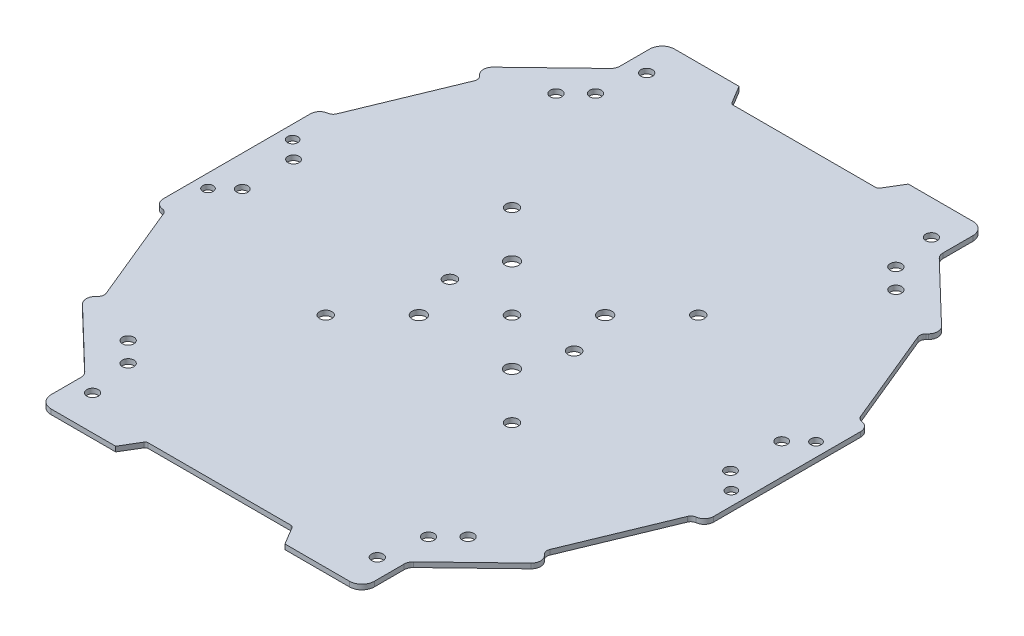
SolidWorks part; units mm, degrees
ref_plane "Front Plane" through (0, 0, 0) normal (0, 0, 1) x (1, 0, 0)
ref_plane "Top Plane" through (0, 0, 0) normal (0, 1, 0) x (1, 0, 0)
ref_plane "Right Plane" through (0, 0, 0) normal (1, 0, 0) x (0, 0, -1)
ref_plane "Plane1"
sketch "Sketch1" plane through (0, 0, 0) normal (0, 1, 0) x (-1, 0, 0)
  line L0 (74.0875, 321.0883) -> (70.3692, 327.2855)
  line L1 (70.3692, 327.2855) -> (45.5805, 327.2855)
  line L2 (45.5805, 327.2855) -> (45.5805, 312.4122)
  line L3 (45.5805, 312.4122) -> (23.246, 290.9343)
  line L4 (23.246, 290.9343) -> (26.6825, 287.3608)
  line L5 (26.6825, 287.3608) -> (12.7354, 253.539)
  line L6 (12.7354, 253.539) -> (9.0171, 253.539)
  line L7 (9.0171, 253.539) -> (9.0171, 226.8911)
  line L8 (9.0171, 226.8911) -> (9.0171, 200.2432)
  line L9 (9.0171, 200.2432) -> (12.7354, 200.2432)
  line L10 (12.7354, 200.2432) -> (26.6825, 166.4214)
  line L11 (26.6825, 166.4214) -> (23.246, 162.8479)
  line L12 (23.246, 162.8479) -> (45.5805, 141.37)
  line L13 (45.5805, 141.37) -> (45.5805, 126.4967)
  line L14 (45.5805, 126.4967) -> (70.3692, 126.4967)
  line L15 (70.3692, 126.4967) -> (74.0875, 132.6939)
  line L16 (74.0875, 132.6939) -> (97.6368, 132.6939)
  line L17 (97.6368, 132.6939) -> (121.1861, 132.6939)
  line L18 (121.1861, 132.6939) -> (124.9044, 126.4967)
  line L19 (124.9044, 126.4967) -> (149.6932, 126.4967)
  line L20 (149.6932, 126.4967) -> (149.6932, 141.37)
  line L21 (149.6932, 141.37) -> (172.0276, 162.8479)
  line L22 (172.0276, 162.8479) -> (168.5911, 166.4214)
  line L23 (168.5911, 166.4214) -> (182.5382, 200.2432)
  line L24 (182.5382, 200.2432) -> (186.2565, 200.2432)
  line L25 (186.2565, 200.2432) -> (186.2565, 226.8911)
  line L26 (186.2565, 226.8911) -> (186.2565, 253.539)
  line L27 (186.2565, 253.539) -> (182.5382, 253.539)
  line L28 (182.5382, 253.539) -> (168.5911, 287.3608)
  line L29 (168.5911, 287.3608) -> (172.0276, 290.9343)
  line L30 (172.0276, 290.9343) -> (149.6932, 312.4122)
  line L31 (149.6932, 312.4122) -> (149.6932, 327.2855)
  line L32 (149.6932, 327.2855) -> (124.9044, 327.2855)
  line L33 (124.9044, 327.2855) -> (121.1861, 321.0883)
  line L34 (121.1861, 321.0883) -> (97.6368, 321.0883)
  line L35 (97.6368, 321.0883) -> (74.0875, 321.0883)
  line L36 (97.6368, 132.6939) -> (97.6368, 321.0883) construction
  line L37 (9.0171, 226.8911) -> (186.2565, 226.8911) construction
  line L38 (67.6368, 256.8911) -> (127.6368, 196.8911) construction
  line L39 (127.6368, 256.8911) -> (67.6368, 196.8911) construction
  line L40 (42.8881, 295.782) -> (49.2662, 302.1601) construction
  line L41 (146.0075, 302.1601) -> (152.3856, 295.782) construction
  line L42 (49.2662, 151.6221) -> (42.8881, 158.0002) construction
  line L43 (146.0075, 151.6221) -> (152.3856, 158.0002) construction
  line L126 (176.3908, 226.8911) -> (176.3908, 225.1916)
  circle A0 centre (112.6368, 211.8911) radius 2.2
  circle A1 centre (49.2662, 151.6221) radius 1.8592
  circle A2 centre (112.6368, 241.8911) radius 2.2
  circle A3 centre (82.6368, 241.8911) radius 2.2
  circle A4 centre (82.6368, 211.8911) radius 2.2
  circle A5 centre (117.6368, 226.8911) radius 2
  circle A6 centre (77.6368, 226.8911) radius 2
  circle A7 centre (97.6368, 226.8911) radius 2
  circle A8 centre (176.2565, 218.6411) radius 1.8
  circle A9 centre (176.2565, 235.1411) radius 1.8
  circle A10 centre (19.0171, 218.6411) radius 1.8
  circle A11 centre (19.0171, 235.1411) radius 1.8
  circle A22 centre (51.7777, 316.1305) radius 1.8592
  circle A23 centre (49.2662, 302.1601) radius 1.8592
  circle A24 centre (13.3551, 240.5249) radius 1.6732
  circle A27 centre (143.496, 137.6517) radius 1.8592
  circle A28 centre (146.0075, 151.6221) radius 1.8592
  circle A30 centre (143.496, 316.1305) radius 1.8592
  circle A33 centre (181.9185, 240.5249) radius 1.6732
  circle A54 centre (146.0075, 302.1601) radius 1.8592
  circle A55 centre (181.9185, 213.2573) radius 1.6732
  circle A74 centre (13.3551, 213.2573) radius 1.6732
  circle A77 centre (51.7777, 137.6517) radius 1.8592
  circle A78 centre (67.6368, 196.8911) radius 1.9831
  circle A79 centre (67.6368, 256.8911) radius 1.9831
  circle A82 centre (42.8881, 158.0002) radius 1.8592
  circle A86 centre (152.3856, 295.782) radius 1.8592
  circle A87 centre (42.8881, 295.782) radius 1.8592
  circle A90 centre (127.6368, 256.8911) radius 1.9831
  circle A91 centre (152.3856, 158.0002) radius 1.8592
  circle A96 centre (127.6368, 196.8911) radius 1.9831
  point P56 (0, 0)
  point P59 (170.4414, 226.3617)
  dimension "D1" = 30
  dimension "D11" = 15
  dimension "D14" = 40
  dimension "D28" = 6.1972
  dimension "D2" = 30
  dimension "D3" = 30
  dimension "D4" = 30
  dimension "D5" = 15
  dimension "D6" = 15
  dimension "D7" = 30
  dimension "D8" = 30
  dimension "D9" = 30
  dimension "D10" = 30
  dimension "D12" = 30
  dimension "D13" = 15
  dimension "D15" = 20
  dimension "D16" = 9.02
  dimension "D17" = 9.02
  dimension "D18" = 9.02
  dimension "D19" = 9.02
  dimension "D20" = 10
  dimension "D21" = 10
  dimension "D22" = 10
  dimension "D23" = 10
  dimension "D24" = 45
  dimension "D25" = 45
  dimension "D26" = 45
  dimension "D27" = 45
  dimension "D29" = 10
  dimension "D30" = 16.5
  dimension "D31" = 8.25
extrude "Extrusion1" add sketch "Sketch1" along normal blind 1.6
fillet "Fillet1" radius 1 4 edges at (-121.1861, 0.8, 132.6939) (-74.0875, 0.8, 132.6939) (-74.0875, 0.8, 321.0883) (-121.1861, 0.8, 321.0883)
fillet "Fillet2" radius 4 4 edges at (-149.6932, 0.8, 126.4967) (-45.5805, 0.8, 126.4967) (-149.6932, 0.8, 327.2855) (-45.5805, 0.8, 327.2855)
fillet "Fillet3" radius 3 4 edges at (-149.6932, 0.8, 141.37) (-45.5805, 0.8, 141.37) (-45.5805, 0.8, 312.4122) (-149.6932, 0.8, 312.4122)
fillet "Fillet4" radius 3 1 edges at (-172.0276, 0.8, 290.9343)
fillet "Fillet5" radius 2 1 edges at (-168.5911, 0.8, 287.3608)
fillet "Fillet6" radius 2 1 edges at (-26.6825, 0.8, 287.3608)
fillet "Fillet7" radius 3 1 edges at (-23.246, 0.8, 290.9343)
fillet "Fillet8" radius 3 2 edges at (-172.0276, 0.8, 162.8479) (-23.246, 0.8, 162.8479)
fillet "Fillet9" radius 2 2 edges at (-26.6825, 0.8, 166.4214) (-168.5911, 0.8, 166.4214)
fillet "Fillet10" radius 2 4 edges at (-12.7354, 0.8, 200.2432) (-12.7354, 0.8, 253.539) (-182.5382, 0.8, 253.539) (-182.5382, 0.8, 200.2432)
fillet "Fillet11" radius 3 4 edges at (-186.2565, 0.8, 200.2432) (-186.2565, 0.8, 253.539) (-9.0171, 0.8, 253.539) (-9.0171, 0.8, 200.2432)
